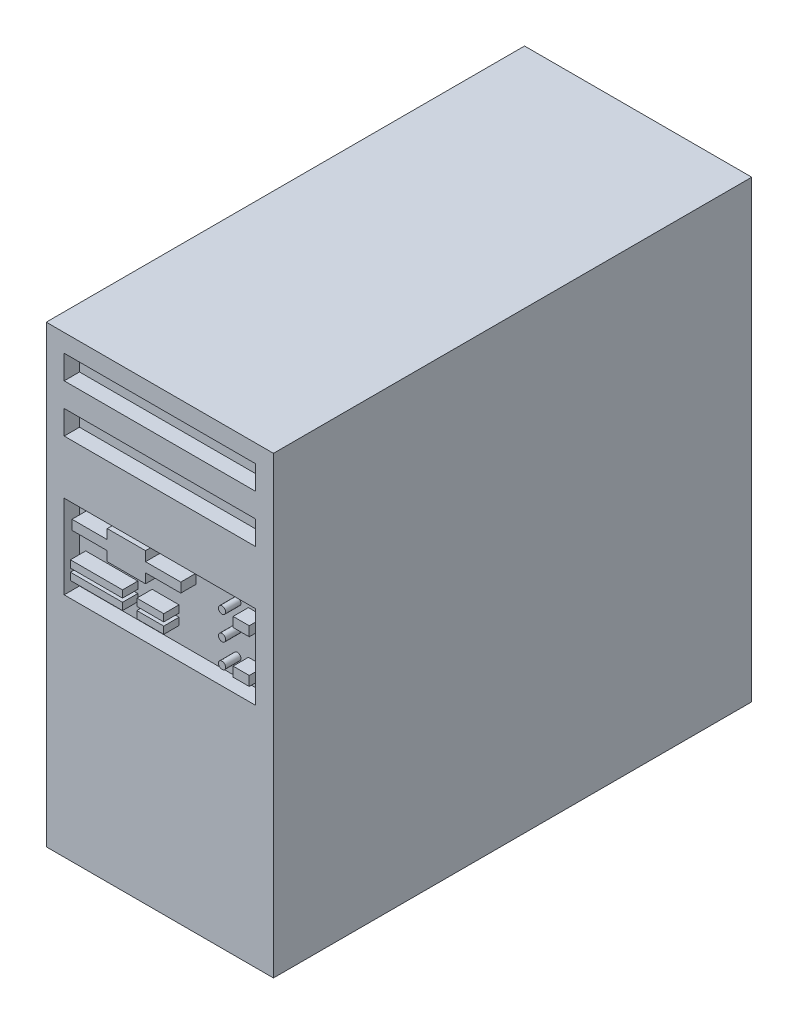
SolidWorks part; units mm, degrees
ref_plane "Front Plane" through (0, 0, 0) normal (0, 0, 1) x (1, 0, 0)
ref_plane "Top Plane" through (0, 0, 0) normal (0, 1, 0) x (1, 0, 0)
ref_plane "Right Plane" through (0, 0, 0) normal (1, 0, 0) x (0, 0, -1)
sketch "Croquis1" plane through (0, 0, 0) normal (1, 0, 0) x (0, 0, -1)
  line L1 (200, -190) -> (-200, -190)
  line L2 (200, -190) -> (200, 190)
  line L3 (200, 190) -> (-200, 190)
  line L4 (-200, -190) -> (-200, 190)
  line L5 (200, -190) -> (-200, 190) construction
  line L6 (200, 190) -> (-200, -190) construction
  point P0 (0, 0)
  dimension "D1" = 400
  dimension "D2" = 380
extrude "Saliente-Extruir1" add sketch "Croquis1" along normal mid plane 190
sketch "Croquis2" plane through (0, 0, -200) normal (0, 0, -1) x (-1, 0, 0)
  line L0 (0, 0) -> (0, 90) construction
  line L1 (0, 90) -> (-25, 90) construction
  line L2 (-25, 90) -> (-25, -70)
  line L3 (-25, -70) -> (30, -70)
  line L4 (30, -70) -> (30, -165)
  line L5 (30, -165) -> (-85, -165)
  line L6 (-85, -165) -> (-85, 90)
  line L7 (-85, 90) -> (-25, 90)
  line L8 (0, 0) -> (0, 160) construction
  line L9 (0, 160) -> (-55, 160) construction
  line L10 (-55, 160) -> (-68, 160) construction
  line L11 (-39.8, 149.15) -> (-70.2, 149.15)
  line L12 (-39.8, 149.15) -> (-39.8, 170.85)
  line L13 (-39.8, 170.85) -> (-70.2, 170.85)
  line L14 (-70.2, 149.15) -> (-70.2, 170.85)
  line L15 (-39.8, 149.15) -> (-70.2, 170.85) construction
  line L16 (-39.8, 170.85) -> (-70.2, 149.15) construction
  line L17 (-68, 160) -> (-68, 164.6699)
  line L18 (-68, 164.6699) -> (-62.5, 169)
  line L19 (-62.5, 169) -> (-47.5, 169)
  line L20 (-47.5, 169) -> (-42, 164.6699)
  line L21 (-42, 164.6699) -> (-42, 160)
  line L22 (-42, 160) -> (-42, 151)
  line L23 (-42, 151) -> (-68, 151)
  line L24 (-68, 151) -> (-68, 160)
  line L25 (-55, 160) -> (-55, 162.8569) construction
  line L26 (-55, 160) -> (-55, 155) construction
  line L27 (-54.5, 165.3569) -> (-55.5, 165.3569)
  line L28 (-54.5, 165.3569) -> (-54.5, 160.3569)
  line L29 (-54.5, 160.3569) -> (-55.5, 160.3569)
  line L30 (-55.5, 165.3569) -> (-55.5, 160.3569)
  line L31 (-54.5, 165.3569) -> (-55.5, 160.3569) construction
  line L32 (-54.5, 160.3569) -> (-55.5, 165.3569) construction
  line L33 (-55, 155) -> (-61.5, 155) construction
  line L34 (-55, 155) -> (-48.5, 155) construction
  line L36 (-61, 152.5) -> (-62, 152.5)
  line L37 (-61, 152.5) -> (-61, 157.5)
  line L38 (-61, 157.5) -> (-62, 157.5)
  line L39 (-62, 152.5) -> (-62, 157.5)
  line L40 (-61, 152.5) -> (-62, 157.5) construction
  line L41 (-61, 157.5) -> (-62, 152.5) construction
  line L42 (-48, 152.5) -> (-49, 152.5)
  line L43 (-48, 152.5) -> (-48, 157.5)
  line L44 (-48, 157.5) -> (-49, 157.5)
  line L45 (-49, 152.5) -> (-49, 157.5)
  line L46 (-48, 152.5) -> (-49, 157.5) construction
  line L47 (-48, 157.5) -> (-49, 152.5) construction
  dimension "D1" = 25
  dimension "D2" = 90
  dimension "D3" = 55
  dimension "D4" = 115
  dimension "D5" = 160
  dimension "D6" = 95
  dimension "D7" = 30.4
  dimension "D8" = 21.7
  dimension "D9" = 6.5
  dimension "D10" = 1
  dimension "D11" = 5
  dimension "D12" = 160
  dimension "D13" = 55
  dimension "D14" = 15
  dimension "D15" = 5
  dimension "D16" = 9
  dimension "D17" = 13
  dimension "D18" = 13
  dimension "D19" = 9
  dimension "D20" = 7
extrude "Cortar-Extruir1" cut sketch "Croquis2" against normal blind 14 contours L14 L11 L12 L13 L23 L24 L17 L18 L19 L20 L21 L22 | L27 L30 L29 L28 | L45 L42 L43 L44 | L39 L36 L37 L38 | L7 L2 L3 L4 L5 L6
sketch "Croquis3" plane through (0, 0, -186) normal (0, 0, -1) x (-1, 0, 0)
  line L0 (-55, 90) -> (-55, 12.5) construction
  line L1 (-55, 12.5) -> (-58, 12.5) construction
  line L2 (2.5, -70) -> (2.5, -85) construction
  line L3 (-35.5, -62.5) -> (-80.5, -62.5)
  line L4 (-35.5, -62.5) -> (-35.5, 87.5)
  line L5 (-35.5, 87.5) -> (-80.5, 87.5)
  line L6 (-85, 90) -> (-85, -165)
  line L7 (-85, -165) -> (30, -165)
  line L8 (30, -165) -> (30, -70)
  line L9 (30, -70) -> (-25, -70)
  line L10 (-25, -70) -> (-25, 90)
  line L11 (-25, 90) -> (-85, 90)
  line L12 (-85, 90) -> (-85, -165)
  line L13 (-85, -165) -> (30, -165)
  line L14 (30, -165) -> (30, -70)
  line L15 (30, -70) -> (-25, -70)
  line L16 (-25, -70) -> (-25, 90)
  line L17 (-25, 90) -> (-85, 90)
  line L18 (-80.5, -62.5) -> (-80.5, 87.5)
  line L19 (-35.5, -62.5) -> (-80.5, 87.5) construction
  line L20 (-35.5, 87.5) -> (-80.5, -62.5) construction
  line L21 (2.5, -85) -> (-22.5, -85) construction
  line L23 (27.5, -92.5) -> (-72.5, -92.5)
  line L24 (27.5, -92.5) -> (27.5, -77.5)
  line L25 (27.5, -77.5) -> (-72.5, -77.5)
  line L26 (-72.5, -92.5) -> (-72.5, -77.5)
  line L27 (27.5, -92.5) -> (-72.5, -77.5) construction
  line L28 (27.5, -77.5) -> (-72.5, -92.5) construction
  dimension "D2" = 77.5
  dimension "D3" = 3
  dimension "D4" = 150
  dimension "D5" = 45
  dimension "D6" = 15
  dimension "D7" = 25
  dimension "D8" = 15
  dimension "D9" = 100
  dimension "D1" = 0
extrude "Saliente-Extruir2" add sketch "Croquis3" along normal blind 3 contours L4 L3 L18 L5 | L24 L23 L26 L25
sketch "Croquis4" plane through (0, 0, -189) normal (0, 0, -1) x (-1, 0, 0)
  line L0 (-58, 87.5) -> (-58, 76) construction
  line L1 (-35.5, 87.5) -> (-80.5, 87.5) construction
  line L2 (-58, 76) -> (-69, 76) construction
  line L3 (-58, 76) -> (-50, 76) construction
  line L4 (-58, 76) -> (-58, 46) construction
  line L5 (-58, 46) -> (-63, 46) construction
  line L6 (-58, 46) -> (-58, 34.3) construction
  line L7 (-58, 34.3) -> (-54, 34.3) construction
  line L8 (-63, 38.25) -> (-63, 53.75) construction
  line L9 (-65.2693, 53.4417) -> (-70.4693, 52.7352)
  line L10 (-65.2693, 38.5583) -> (-70.4693, 39.2648)
  line L11 (-72.2, 50.7534) -> (-72.2, 41.2466)
  line L12 (-63, 40.5401) -> (-63, 51.4599)
  line L13 (-54, 15.8) -> (-54, 52.8) construction
  line L14 (-52.3686, 53.1059) -> (-48.3686, 53.8559)
  line L15 (-46, 51.8901) -> (-46, 16.7099)
  line L16 (-63, 38.25) -> (-72.2, 38.25) construction
  line L17 (-72.2, 38.25) -> (-72.2, 39.5) construction
  line L18 (-63, 53.75) -> (-72.2, 53.75) construction
  line L19 (-72.2, 53.75) -> (-72.2, 52.5) construction
  line L20 (-72.2, 38.25) -> (-72.2, 39.5) construction
  line L21 (-48.3686, 14.7441) -> (-52.3686, 15.4941)
  line L22 (-46, 54.3) -> (-54, 54.3) construction
  line L23 (-54, 54.3) -> (-54, 52.8) construction
  line L24 (-46, 14.3) -> (-54, 14.3) construction
  line L25 (-54, 14.3) -> (-54, 15.8) construction
  line L26 (-54, 51.1401) -> (-54, 17.4599)
  line L27 (-58, 34.3) -> (-58, 13.5) construction
  line L28 (-58, 13.5) -> (-65, 13.5) construction
  line L29 (-68.25, 23) -> (-70, 23)
  line L30 (-60, 4) -> (-61.75, 4)
  line L31 (-60, 4) -> (-60, 23)
  line L32 (-60, 23) -> (-61.75, 23)
  line L33 (-70, 4) -> (-70, 23)
  line L34 (-60, 4) -> (-70, 23) construction
  line L35 (-60, 23) -> (-70, 4) construction
  line L36 (-68.25, 4) -> (-70, 4)
  line L37 (-35.5, 87.5) -> (-80.5, 87.5) construction
  line L38 (-68.25, 4) -> (-68.25, 23) construction
  line L39 (-61.75, 23) -> (-61.75, 4) construction
  line L40 (-58, 13.5) -> (-58, -13.5) construction
  line L41 (-58, -13.5) -> (-51, -13.5) construction
  line L42 (-58, -13.5) -> (-63, -13.5) construction
  line L43 (-63, -13.5) -> (-71, -13.5) construction
  line L44 (-58, -13.5) -> (-58, -40.5) construction
  line L45 (-58, -40.5) -> (-63, -40.5) construction
  line L46 (-63, -40.5) -> (-71, -40.5) construction
  line L47 (-71, -13.5) -> (-71, -40.5) construction
  line L48 (-63, -13.5) -> (-63, -40.5) construction
  line L49 (-58, -40.5) -> (-50, -40.5) construction
  line L50 (-58, -40.5) -> (-58, -57.5) construction
  line L51 (-58, -57.5) -> (-68, -57.5) construction
  line L52 (-58, -57.5) -> (-56, -57.5) construction
  line L53 (-56, -57.5) -> (-43, -57.5) construction
  line L55 (-60.5, -20) -> (-65.5, -20)
  line L56 (-60.5, -20) -> (-60.5, -7)
  line L57 (-60.5, -7) -> (-65.5, -7)
  line L58 (-65.5, -20) -> (-65.5, -7)
  line L59 (-60.5, -20) -> (-65.5, -7) construction
  line L60 (-60.5, -7) -> (-65.5, -20) construction
  line L61 (-68.5, -20) -> (-73.5, -20)
  line L62 (-68.5, -20) -> (-68.5, -7)
  line L63 (-68.5, -7) -> (-73.5, -7)
  line L64 (-73.5, -20) -> (-73.5, -7)
  line L65 (-68.5, -20) -> (-73.5, -7) construction
  line L66 (-68.5, -7) -> (-73.5, -20) construction
  line L67 (-60.5, -47) -> (-65.5, -47)
  line L68 (-60.5, -47) -> (-60.5, -34)
  line L69 (-60.5, -34) -> (-65.5, -34)
  line L70 (-65.5, -47) -> (-65.5, -34)
  line L71 (-60.5, -47) -> (-65.5, -34) construction
  line L72 (-60.5, -34) -> (-65.5, -47) construction
  line L73 (-68.5, -47) -> (-73.5, -47)
  line L74 (-68.5, -47) -> (-68.5, -34)
  line L75 (-68.5, -34) -> (-73.5, -34)
  line L76 (-73.5, -47) -> (-73.5, -34)
  line L77 (-68.5, -47) -> (-73.5, -34) construction
  line L78 (-68.5, -34) -> (-73.5, -47) construction
  line L79 (-46, -20.5) -> (-56, -20.5) construction
  line L80 (-46, -20.5) -> (-46, -6.5)
  line L81 (-46, -6.5) -> (-56, -6.5)
  line L82 (-56, -20.5) -> (-56, -6.5)
  line L83 (-46, -20.5) -> (-56, -6.5) construction
  line L84 (-46, -6.5) -> (-56, -20.5) construction
  line L85 (-44, -47) -> (-56, -47)
  line L86 (-44, -47) -> (-44, -34)
  line L87 (-44, -34) -> (-56, -34)
  line L88 (-56, -47) -> (-56, -34)
  line L89 (-44, -47) -> (-56, -34) construction
  line L90 (-44, -34) -> (-56, -47) construction
  circle A0 centre (-69, 76) radius 6.15
  circle A1 centre (-50, 76) radius 6.15
  arc A2 (-65.2693, 38.5583) -> (-63, 40.5401) centre (-65, 40.5401) ccw
  arc A3 (-70.4693, 39.2648) -> (-72.2, 41.2466) centre (-70.2, 41.2466) cw
  arc A4 (-70.4693, 52.7352) -> (-72.2, 50.7534) centre (-70.2, 50.7534) ccw
  arc A5 (-65.2693, 53.4417) -> (-63, 51.4599) centre (-65, 51.4599) cw
  arc A6 (-48.3686, 14.7441) -> (-46, 16.7099) centre (-48, 16.7099) ccw
  arc A7 (-54, 17.4599) -> (-52.3686, 15.4941) centre (-52, 17.4599) ccw
  arc A8 (-52.3686, 53.1059) -> (-54, 51.1401) centre (-52, 51.1401) ccw
  arc A9 (-46, 51.8901) -> (-48.3686, 53.8559) centre (-48, 51.8901) ccw
  arc A10 (-61.75, 23) -> (-68.25, 23) centre (-65, 23) ccw
  arc A11 (-68.25, 4) -> (-61.75, 4) centre (-65, 4) ccw
  arc A12 (-56, -20.5) -> (-46, -20.5) centre (-51, -20.5) ccw
  circle A13 centre (-68, -57.5) radius 4
  circle A14 centre (-56, -57.5) radius 4
  circle A15 centre (-43, -57.5) radius 4
  point P14 (-63, 46)
  point P34 (-54, 34.3)
  point P98 (-51, -6.5)
  dimension "D2" = 12.3
  dimension "D3" = 11
  dimension "D10" = 2
  dimension "D16" = 2
  dimension "D17" = 19
  dimension "D18" = 6.5
  dimension "D29" = 14
  dimension "D35" = 8
  dimension "D1" = 11.5
  dimension "D4" = 8
  dimension "D5" = 41.5
  dimension "D6" = 13
  dimension "D7" = 5
  dimension "D8" = 9.2
  dimension "D9" = 15.5
  dimension "D11" = 4
  dimension "D12" = 40
  dimension "D13" = 37
  dimension "D14" = 8
  dimension "D15" = 53.2
  dimension "D19" = 10
  dimension "D20" = 7
  dimension "D21" = 74
  dimension "D22" = 1.75
  dimension "D23" = 5
  dimension "D24" = 8
  dimension "D25" = 5
  dimension "D26" = 13
  dimension "D27" = 101
  dimension "D28" = 128
  dimension "D30" = 10
  dimension "D31" = 7
  dimension "D32" = 12
  dimension "D33" = 13
  dimension "D34" = 8
  dimension "D36" = 10
  dimension "D37" = 2
  dimension "D38" = 13
  dimension "D39" = 145
extrude "Saliente-Extruir3" add sketch "Croquis4" along normal blind 5
sketch "Croquis5" plane through (0, 0, -189) normal (0, 0, -1) x (-1, 0, 0)
  line L0 (27.5, -85) -> (-13, -85) construction
  line L1 (27.5, -92.5) -> (27.5, -77.5) construction
  line L2 (-13, -85) -> (-28, -85) construction
  line L3 (-28, -85) -> (-48, -85) construction
  line L4 (-48, -85) -> (-48, -81) construction
  line L5 (-42, -81) -> (-54, -81) construction
  line L6 (-54.3787, -82.5149) -> (-55.3787, -86.5149)
  line L7 (-53.4384, -89) -> (-42.5616, -89)
  line L8 (-40.6213, -86.5149) -> (-41.6213, -82.5149)
  line L9 (-40, -89) -> (-40, -81) construction
  line L10 (-40, -81) -> (-42, -81) construction
  line L11 (-54, -81) -> (-56, -81) construction
  line L12 (-56, -81) -> (-56, -89) construction
  line L13 (-52.4384, -81) -> (-43.5616, -81)
  line L14 (-48, -85) -> (-48, -89) construction
  circle A0 centre (-13, -85) radius 4.1
  circle A1 centre (-28, -85) radius 5.55
  arc A2 (-55.3787, -86.5149) -> (-53.4384, -89) centre (-53.4384, -87) ccw
  arc A3 (-42.5616, -89) -> (-40.6213, -86.5149) centre (-42.5616, -87) ccw
  arc A4 (-43.5616, -81) -> (-41.6213, -82.5149) centre (-43.5616, -83) cw
  arc A5 (-52.4384, -81) -> (-54.3787, -82.5149) centre (-52.4384, -83) ccw
  point P12 (-48, -81)
  dimension "D6" = 2
  dimension "D7" = 8.2
  dimension "D8" = 11.1
  dimension "D1" = 40.5
  dimension "D2" = 15
  dimension "D3" = 20
  dimension "D4" = 12
  dimension "D5" = 16
  dimension "D9" = 8
extrude "Saliente-Extruir4" add sketch "Croquis5" along normal blind 5
sketch "Croquis6" plane through (0, 0, 200) normal (0, 0, 1) x (1, 0, 0)
  line L0 (0, 0) -> (0, 35) construction
  line L1 (80, 35) -> (68, 35) construction
  line L2 (80, 70) -> (-80, 70)
  line L3 (80, 70) -> (80, 0)
  line L4 (80, 0) -> (-80, 0)
  line L5 (-80, 70) -> (-80, 0)
  line L6 (80, 70) -> (-80, 0) construction
  line L7 (80, 0) -> (-80, 70) construction
  line L8 (68, 35) -> (52, 35) construction
  line L9 (-53, 25) -> (-53, 16) construction
  line L10 (68, 35) -> (68, 15) construction
  line L11 (68, 35) -> (68, 51) construction
  line L12 (74.75, 11) -> (61.25, 11)
  line L13 (74.75, 11) -> (74.75, 19)
  line L14 (74.75, 19) -> (61.25, 19)
  line L15 (61.25, 11) -> (61.25, 19)
  line L16 (74.75, 11) -> (61.25, 19) construction
  line L17 (74.75, 19) -> (61.25, 11) construction
  line L18 (52, 35) -> (52, 55) construction
  line L19 (74.75, 47) -> (61.25, 47)
  line L20 (74.75, 47) -> (74.75, 55)
  line L21 (74.75, 55) -> (61.25, 55)
  line L22 (61.25, 47) -> (61.25, 55)
  line L23 (74.75, 47) -> (61.25, 55) construction
  line L24 (74.75, 55) -> (61.25, 47) construction
  line L25 (52, 35) -> (52, 15) construction
  line L26 (52, 35) -> (52, 15) construction
  line L27 (52, 15) -> (68, 15) construction
  line L28 (0, 35) -> (0, 54) construction
  line L29 (0, 54) -> (-28, 54) construction
  line L30 (0, 35) -> (-8, 35) construction
  line L31 (17.5, 50) -> (-73.5, 50)
  line L32 (17.5, 50) -> (17.5, 58)
  line L33 (17.5, 58) -> (-73.5, 58)
  line L34 (-73.5, 50) -> (-73.5, 58)
  line L35 (17.5, 50) -> (-73.5, 58) construction
  line L36 (17.5, 58) -> (-73.5, 50) construction
  line L37 (-12, 42) -> (-44, 42)
  line L38 (-12, 42) -> (-12, 66)
  line L39 (-12, 66) -> (-44, 66)
  line L40 (-44, 42) -> (-44, 66)
  line L41 (-12, 42) -> (-44, 66) construction
  line L42 (-12, 66) -> (-44, 42) construction
  line L43 (-8, 35) -> (-8, 25) construction
  line L44 (-8, 25) -> (-8, 16) construction
  line L45 (-8, 25) -> (-53, 25) construction
  line L46 (-8, 16) -> (-53, 16) construction
  line L47 (3.25, 22) -> (-19.25, 22)
  line L48 (3.25, 22) -> (3.25, 28)
  line L49 (3.25, 28) -> (-19.25, 28)
  line L50 (-19.25, 22) -> (-19.25, 28)
  line L51 (3.25, 22) -> (-19.25, 28) construction
  line L52 (3.25, 28) -> (-19.25, 22) construction
  line L53 (3.25, 13) -> (-19.25, 13)
  line L54 (3.25, 13) -> (3.25, 19)
  line L55 (3.25, 19) -> (-19.25, 19)
  line L56 (-19.25, 13) -> (-19.25, 19)
  line L57 (3.25, 13) -> (-19.25, 19) construction
  line L58 (3.25, 19) -> (-19.25, 13) construction
  line L59 (-31.2, 22) -> (-74.8, 22)
  line L60 (-31.2, 22) -> (-31.2, 28)
  line L61 (-31.2, 28) -> (-74.8, 28)
  line L62 (-74.8, 22) -> (-74.8, 28)
  line L63 (-31.2, 22) -> (-74.8, 28) construction
  line L64 (-31.2, 28) -> (-74.8, 22) construction
  line L65 (-31.2, 13) -> (-74.8, 13)
  line L66 (-31.2, 13) -> (-31.2, 19)
  line L67 (-31.2, 19) -> (-74.8, 19)
  line L68 (-74.8, 13) -> (-74.8, 19)
  line L69 (-31.2, 13) -> (-74.8, 19) construction
  line L70 (-31.2, 19) -> (-74.8, 13) construction
  line L71 (0, 35) -> (0, 125) construction
  line L72 (0, 125) -> (0, 165) construction
  line L74 (80, 155) -> (-80, 155)
  line L75 (80, 155) -> (80, 175)
  line L76 (80, 175) -> (-80, 175)
  line L77 (-80, 155) -> (-80, 175)
  line L78 (80, 155) -> (-80, 175) construction
  line L79 (80, 175) -> (-80, 155) construction
  line L80 (80, 115) -> (-80, 115)
  line L81 (80, 115) -> (80, 135)
  line L82 (80, 135) -> (-80, 135)
  line L83 (-80, 115) -> (-80, 135)
  line L84 (80, 115) -> (-80, 135) construction
  line L85 (80, 135) -> (-80, 115) construction
  circle A0 centre (52, 35) radius 3
  circle A1 centre (52, 55) radius 3
  circle A2 centre (52, 15) radius 3
  point P56 (-31.2, 16)
  point P57 (-19.25, 25)
  dimension "D10" = 6
  dimension "D1" = 35
  dimension "D2" = 70
  dimension "D3" = 160
  dimension "D4" = 12
  dimension "D5" = 16
  dimension "D6" = 13.5
  dimension "D7" = 8
  dimension "D8" = 20
  dimension "D9" = 16
  dimension "D11" = 20
  dimension "D12" = 91
  dimension "D13" = 8
  dimension "D14" = 28
  dimension "D15" = 24
  dimension "D16" = 32
  dimension "D17" = 19
  dimension "D18" = 10
  dimension "D19" = 43.6
  dimension "D20" = 45
  dimension "D21" = 8
  dimension "D22" = 22.5
  dimension "D23" = 6
  dimension "D24" = 9
  dimension "D25" = 90
  dimension "D26" = 20
  dimension "D27" = 40
extrude "Cortar-Extruir2" cut sketch "Croquis6" against normal blind 12.8 contours L77 L74 L75 L76 | L83 L80 L81 L82 | L2 L5 L4 L3 A2 A1 A0 L12 L15 L14 L13 L19 L22 L21 L20 L37 L40 L31 L34 L33 L39 L38 L32 L47 L50 L49 L48 L53 L56 L55 L54 L59 L62 L61 L60 L65 L68
